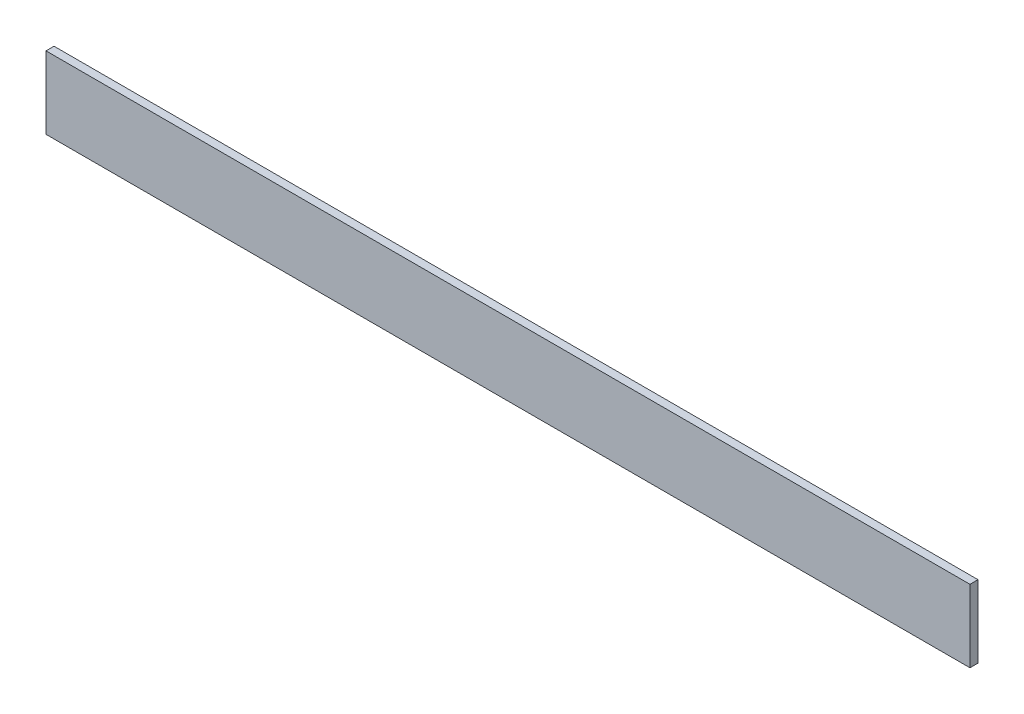
SolidWorks part; units mm, degrees
ref_plane "Front" through (0, 0, 0) normal (0, 0, 1) x (1, 0, 0)
ref_plane "Top" through (0, 0, 0) normal (0, 1, 0) x (1, 0, 0)
ref_plane "Right" through (0, 0, 0) normal (1, 0, 0) x (0, 0, -1)
sketch "Sketch1" plane through (0, 0, 0) normal (0, 0, 1) x (1, 0, 0)
  line L1 (1150, 90) -> (-1150, 90)
  line L2 (1150, 90) -> (1150, -90)
  line L3 (1150, -90) -> (-1150, -90)
  line L4 (-1150, 90) -> (-1150, -90)
  line L5 (1150, 90) -> (-1150, -90) construction
  line L6 (1150, -90) -> (-1150, 90) construction
  point P1 (0, 0)
  dimension "D1" = 2300
  dimension "D2" = 180
extrude "Boss-Extrude1" add sketch "Sketch1" along normal mid plane 20
